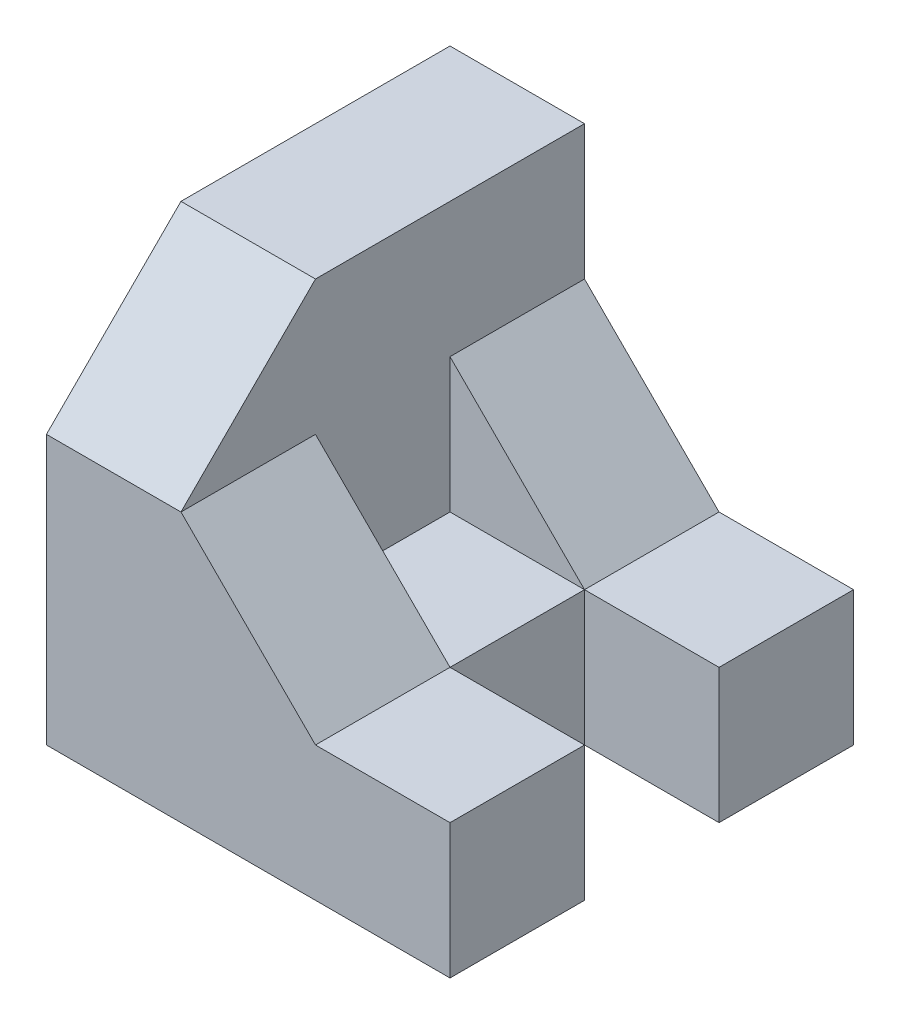
SolidWorks part; units mm, degrees
ref_plane "Alzado" through (0, 0, 0) normal (0, 0, 1) x (1, 0, 0)
ref_plane "Planta" through (0, 0, 0) normal (0, 1, 0) x (1, 0, 0)
ref_plane "Vista lateral" through (0, 0, 0) normal (1, 0, 0) x (0, 0, -1)
sketch "Croquis1" plane through (0, 0, 0) normal (0, 1, 0) x (1, 0, 0)
  line L1 (0, 0) -> (60, 0)
  line L2 (0, 0) -> (0, -60)
  line L3 (0, -60) -> (60, -60)
  line L4 (60, 0) -> (60, -60)
  dimension "D1" = 60
  dimension "D2" = 60
extrude "Saliente-Extruir1" add sketch "Croquis1" along normal blind 60
sketch "Croquis2" plane through (0, 60, 0) normal (0, 1, 0) x (1, 0, 0)
  line L0 (0, -60) -> (60, -60) construction
  line L1 (60, 0) -> (20, 0)
  line L2 (60, 0) -> (60, -60)
  line L3 (60, -60) -> (20, -60)
  line L4 (20, 0) -> (20, -60)
  dimension "D1" = 40
extrude "Cortar-Extruir1" cut sketch "Croquis2" against normal blind 20
sketch "Croquis3" plane through (0, 40, 0) normal (0, 1, 0) x (1, 0, 0)
  line L0 (20, -60) -> (60, -60) construction
  line L1 (60, 0) -> (40, 0)
  line L2 (60, 0) -> (60, -60)
  line L3 (60, -60) -> (40, -60)
  line L4 (40, 0) -> (40, -60)
  dimension "D1" = 20
extrude "Cortar-Extruir2" cut sketch "Croquis3" against normal blind 20
sketch "Croquis4" plane through (20, 0, 0) normal (1, 0, 0) x (0, 0, -1)
  line L0 (-60, 40) -> (-60, 60)
  line L1 (-60, 60) -> (-40, 60)
  line L2 (0, 60) -> (-60, 60) construction
  line L3 (-40, 60) -> (-60, 40)
extrude "Cortar-Extruir3" cut sketch "Croquis4" against normal blind 20
sketch "Croquis5" plane through (0, 0, 60) normal (0, 0, 1) x (1, 0, 0)
  line L0 (20, 40) -> (40, 20)
  line L1 (40, 20) -> (40, 40)
  line L2 (40, 40) -> (20, 40)
sketch "Croquis7" plane through (0, 40, 0) normal (0, 1, 0) x (1, 0, 0)
  line L0 (40, 0) -> (40, -60) construction
  line L1 (20, 0) -> (40, 0)
  line L2 (20, 0) -> (20, -20)
  line L3 (20, -20) -> (40, -20)
  line L4 (40, 0) -> (40, -20)
  line L5 (20, -20) -> (20, -40)
  line L6 (20, -20) -> (40, -20)
  line L7 (40, -20) -> (40, -40)
  line L8 (20, -40) -> (40, -40)
  dimension "D1" = 20
  dimension "D2" = 2
extrude "Cortar-Extruir5" cut sketch "Croquis7" against normal blind 20 contours L5 L8 L7 L6
extrude "Cortar-Extruir6" cut sketch "Croquis5" against normal blind 60
sketch "Croquis8" plane through (0, 20, 0) normal (0, 1, 0) x (1, 0, 0)
  line L0 (40, -20) -> (40, -40)
  line L1 (40, -40) -> (60, -40)
  line L2 (60, -60) -> (60, 0) construction
  line L3 (60, -40) -> (60, -20)
  line L4 (60, -20) -> (40, -20)
extrude "Cortar-Extruir7" cut sketch "Croquis8" against normal blind 60
